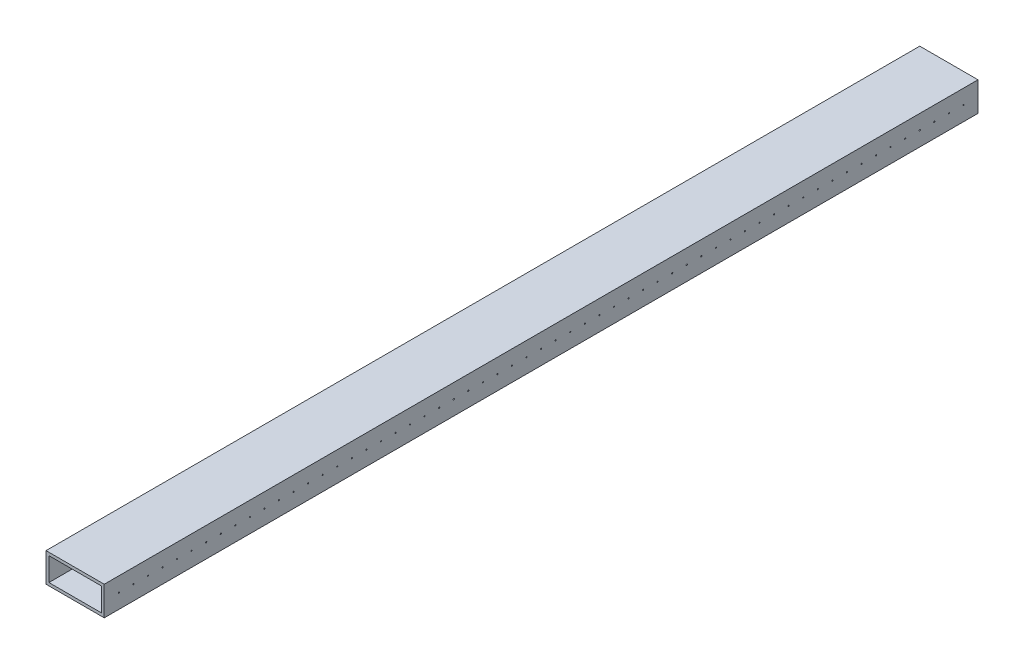
SolidWorks part; units mm, degrees
ref_plane "Front Plane" through (0, 0, 0) normal (0, 0, 1) x (1, 0, 0)
ref_plane "Top Plane" through (0, 0, 0) normal (0, 1, 0) x (1, 0, 0)
ref_plane "Right Plane" through (0, 0, 0) normal (1, 0, 0) x (0, 0, -1)
sketch "Sketch1" plane through (0, 0, 0) normal (0, 0, 1) x (1, 0, 0)
  line L0 (2.54, -2.54) -> (2.54, -22.86)
  line L1 (0, 0) -> (50.8, 0)
  line L2 (0, 0) -> (0, -25.4)
  line L3 (0, -25.4) -> (50.8, -25.4)
  line L4 (50.8, 0) -> (50.8, -25.4)
  line L5 (2.54, -22.86) -> (48.26, -22.86)
  line L6 (48.26, -2.54) -> (48.26, -22.86)
  line L7 (2.54, -2.54) -> (48.26, -2.54)
  dimension "D1" = 50.8
  dimension "D2" = 25.4
  dimension "D3" = 2.54
extrude "Boss-Extrude1" add sketch "Sketch1" along normal blind 762
sketch "Sketch2" plane through (50.8, 0, 0) normal (1, 0, 0) x (0, 0, -1)
  line L0 (-762, -12.7) -> (0, -12.7) construction
  line L1 (-762, -25.4) -> (-762, 0) construction
  line L2 (0, -25.4) -> (0, 0) construction
  circle A0 centre (-749.3, -12.7) radius 0.5
  circle A1 centre (-736.6, -12.7) radius 0.5
  circle A2 centre (-723.9, -12.7) radius 0.5
  circle A3 centre (-711.2, -12.7) radius 0.5
  circle A4 centre (-698.5, -12.7) radius 0.5
  circle A5 centre (-685.8, -12.7) radius 0.5
  circle A6 centre (-673.1, -12.7) radius 0.5
  circle A7 centre (-660.4, -12.7) radius 0.5
  circle A8 centre (-647.7, -12.7) radius 0.5
  circle A9 centre (-635, -12.7) radius 0.5
  circle A10 centre (-622.3, -12.7) radius 0.5
  circle A11 centre (-609.6, -12.7) radius 0.5
  circle A12 centre (-596.9, -12.7) radius 0.5
  circle A13 centre (-584.2, -12.7) radius 0.5
  circle A14 centre (-571.5, -12.7) radius 0.5
  circle A15 centre (-558.8, -12.7) radius 0.5
  circle A16 centre (-546.1, -12.7) radius 0.5
  circle A17 centre (-533.4, -12.7) radius 0.5
  circle A18 centre (-520.7, -12.7) radius 0.5
  circle A19 centre (-508, -12.7) radius 0.5
  circle A20 centre (-495.3, -12.7) radius 0.5
  circle A21 centre (-482.6, -12.7) radius 0.5
  circle A22 centre (-469.9, -12.7) radius 0.5
  circle A23 centre (-457.2, -12.7) radius 0.5
  circle A24 centre (-444.5, -12.7) radius 0.5
  circle A25 centre (-431.8, -12.7) radius 0.5
  circle A26 centre (-419.1, -12.7) radius 0.5
  circle A27 centre (-406.4, -12.7) radius 0.5
  circle A28 centre (-393.7, -12.7) radius 0.5
  circle A29 centre (-381, -12.7) radius 0.5
  circle A30 centre (-368.3, -12.7) radius 0.5
  circle A31 centre (-355.6, -12.7) radius 0.5
  circle A32 centre (-342.9, -12.7) radius 0.5
  circle A33 centre (-330.2, -12.7) radius 0.5
  circle A34 centre (-317.5, -12.7) radius 0.5
  circle A35 centre (-304.8, -12.7) radius 0.5
  circle A36 centre (-292.1, -12.7) radius 0.5
  circle A37 centre (-279.4, -12.7) radius 0.5
  circle A38 centre (-266.7, -12.7) radius 0.5
  circle A39 centre (-254, -12.7) radius 0.5
  circle A40 centre (-241.3, -12.7) radius 0.5
  circle A41 centre (-228.6, -12.7) radius 0.5
  circle A42 centre (-215.9, -12.7) radius 0.5
  circle A43 centre (-203.2, -12.7) radius 0.5
  circle A44 centre (-190.5, -12.7) radius 0.5
  circle A45 centre (-177.8, -12.7) radius 0.5
  circle A46 centre (-165.1, -12.7) radius 0.5
  circle A47 centre (-152.4, -12.7) radius 0.5
  circle A48 centre (-139.7, -12.7) radius 0.5
  circle A49 centre (-127, -12.7) radius 0.5
  circle A50 centre (-114.3, -12.7) radius 0.5
  circle A51 centre (-101.6, -12.7) radius 0.5
  circle A52 centre (-88.9, -12.7) radius 0.5
  circle A53 centre (-76.2, -12.7) radius 0.5
  circle A54 centre (-63.5, -12.7) radius 0.5
  circle A55 centre (-50.8, -12.7) radius 0.5
  circle A56 centre (-38.1, -12.7) radius 0.5
  circle A57 centre (-25.4, -12.7) radius 0.5
  circle A58 centre (-12.7, -12.7) radius 0.5
  dimension "D1" = 1
  dimension "D2" = 12.7
  dimension "D3" = 59
extrude "Cut-Extrude1" cut sketch "Sketch2" against normal blind 279.4
